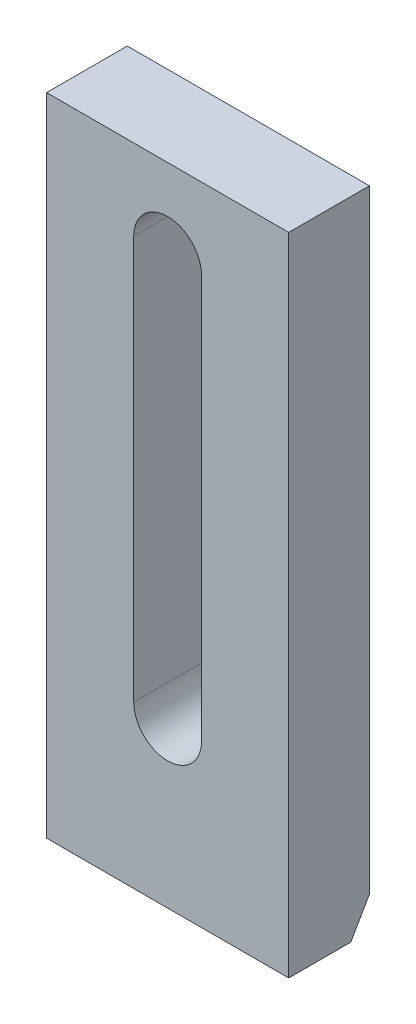
SolidWorks part; units mm, degrees
material "Простая углеродистая сталь"
ref_plane "Спереди" through (0, 0, 0) normal (0, 0, 1) x (1, 0, 0)
ref_plane "Сверху" through (0, 0, 0) normal (0, 1, 0) x (1, 0, 0)
ref_plane "Справа" through (0, 0, 0) normal (1, 0, 0) x (0, 0, -1)
sketch "Эскиз1" plane through (0, 0, 0) normal (0, 0, 1) x (1, 0, 0)
  line L1 (0, 0) -> (75, 0)
  line L2 (0, 0) -> (0, 200)
  line L3 (0, 200) -> (75, 200)
  line L4 (75, 0) -> (75, 200)
  dimension "D1" = 75
  dimension "D2" = 200
extrude "Бобышка-Вытянуть1" add sketch "Эскиз1" along normal blind 25
sketch "Эскиз2" plane through (0, 0, 25) normal (0, 0, 1) x (1, 0, 0)
  line L1 (27, 50) -> (27, 175)
  line L2 (48, 50) -> (48, 175)
  line L3 (0, 200) -> (0, 0) construction
  line L4 (0, 0) -> (75, 0) construction
  arc A0 (27, 50) -> (48, 50) centre (37.5, 50) ccw
  arc A1 (27, 175) -> (48, 175) centre (37.5, 175) cw
  point P7 (27, 112.5)
  point P10 (48, 112.5)
  dimension "D1" = 37.5
  dimension "D2" = 50
extrude "Вырез-Вытянуть1" cut sketch "Эскиз2" against normal through all
chamfer "Фаска1" distance 10 angle 30 1 edges at (37.5, 0, 0)
